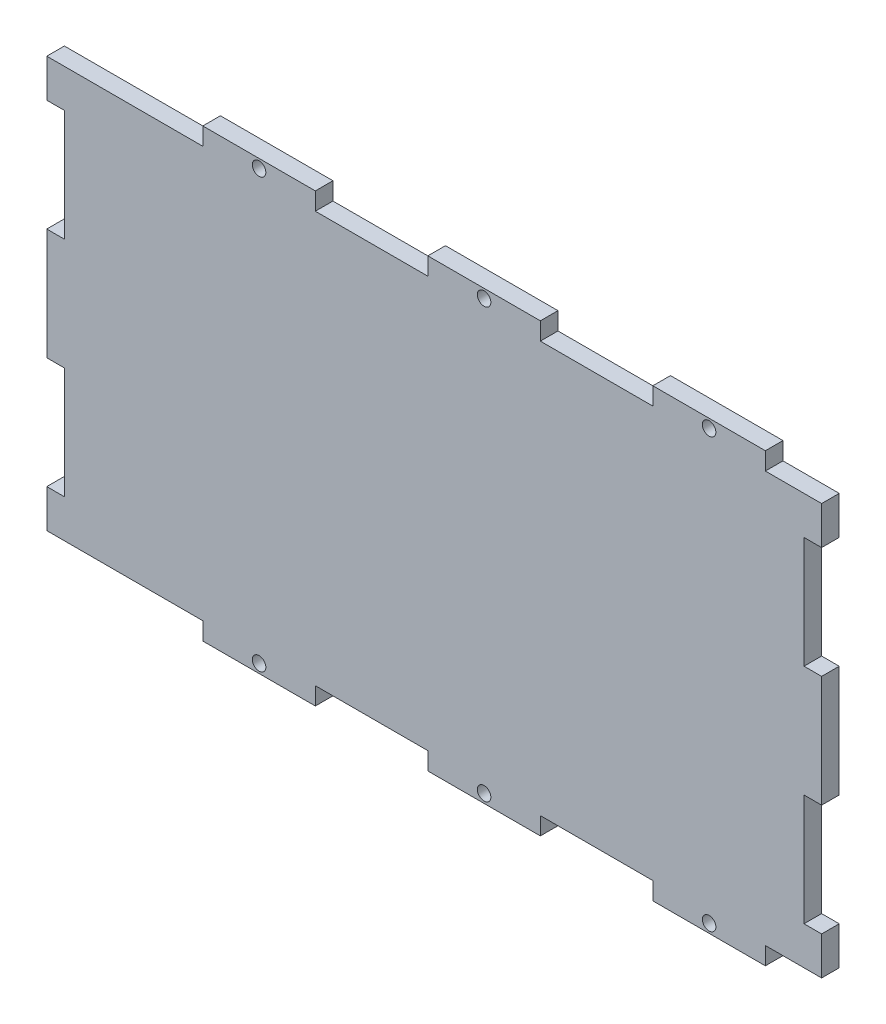
SolidWorks part; units mm, degrees
material "Acrílico (Impacto medio-alto)"
ref_plane "Alzado" through (0, 0, 0) normal (0, 0, 1) x (1, 0, 0)
ref_plane "Planta" through (0, 0, 0) normal (0, 1, 0) x (1, 0, 0)
ref_plane "Vista lateral" through (0, 0, 0) normal (1, 0, 0) x (0, 0, -1)
sketch "Croquis1" plane through (0, 0, 0) normal (0, 0, 1) x (1, 0, 0)
  line L1 (-57.5, -35) -> (57.5, -35)
  line L2 (-57.5, -35) -> (-57.5, 35)
  line L3 (-57.5, 35) -> (57.5, 35)
  line L4 (57.5, -35) -> (57.5, 35)
  line L5 (-57.5, -35) -> (57.5, 35) construction
  line L6 (-57.5, 35) -> (57.5, -35) construction
  point P0 (0, 0)
  dimension "D1" = 70
  dimension "D2" = 115
extrude "Saliente-Extruir1" add sketch "Croquis1" along normal mid plane 3
sketch "Croquis2" plane through (0, 0, 0) normal (0, 0, 1) x (1, 0, 0)
  line L0 (57.5, 35) -> (-57.5, 35) construction
  line L1 (-47.9167, 35) -> (-28.75, 35)
  line L2 (-47.9167, 35) -> (-47.9167, 38)
  line L3 (-47.9167, 38) -> (-28.75, 38)
  line L4 (-28.75, 35) -> (-28.75, 38)
  line L5 (-57.5, 35) -> (-57.5, -35) construction
  circle A0 centre (-38.3333, 36.5) radius 1.15
  point P11 (-28.75, 36.5)
  point P13 (-38.3333, 38)
  dimension "D1" = 3
  dimension "D4" = 2.3
  dimension "D2" = 19.1667
  dimension "D3" = 9.5833
extrude "Saliente-Extruir2" add sketch "Croquis2" along normal mid plane 3
pattern_linear "MatrizL1" count 3 spacing 38.3333 along (1, 0, 0) of "Saliente-Extruir2"
mirror "Simetría1" about plane through (0, 0, 0) normal (0, 1, 0) of "MatrizL1", "Saliente-Extruir2"
sketch "Croquis3" plane through (0, 0, 0) normal (0, 0, 1) x (1, 0, 0)
  line L0 (57.5, -35) -> (57.5, 35) construction
  line L1 (57.5, 28.5) -> (54.5, 28.5)
  line L2 (57.5, 28.5) -> (57.5, 9.5)
  line L3 (57.5, 9.5) -> (54.5, 9.5)
  line L4 (54.5, 28.5) -> (54.5, 20.15)
  line L5 (54.5, 17.85) -> (51.5, 17.85) construction
  line L6 (51.5, 17.85) -> (51.5, 20.15) construction
  line L7 (51.5, 20.15) -> (54.5, 20.15) construction
  line L8 (54.5, 17.85) -> (54.5, 9.5)
  line L9 (54.5, 20.15) -> (54.5, 17.85)
  line L10 (9.5833, 38) -> (-9.5833, 38) construction
  point P8 (51.5, 19)
  point P11 (57.5, 19)
  dimension "D1" = 2.3
  dimension "D2" = 3
  dimension "D3" = 3
  dimension "D5" = 19
  dimension "D4" = 9.5
extrude "Cortar-Extruir1" cut sketch "Croquis3" against normal through all both and the other way through all
pattern_linear "MatrizL2" count 2 spacing 38 along (0, -1, 0) of "Cortar-Extruir1"
mirror "Simetría2" about plane through (0, 0, 0) normal (1, 0, 0) of "MatrizL2", "Cortar-Extruir1"
sketch "Croquis4" plane through (-57.5, 0, 0) normal (-1, 0, 0) x (0, 0, 1)
  line L0 (1.5, -28.5) -> (-1.5, -28.5) construction
  line L1 (-1.5, -28.5) -> (-1.5, -35) construction
  line L2 (-1.5, -35) -> (1.5, -35) construction
  line L3 (1.5, -35) -> (1.5, -28.5) construction
  line L4 (-1.5, 28.5) -> (1.5, 28.5) construction
  line L5 (1.5, 28.5) -> (1.5, 35) construction
  line L6 (1.5, 35) -> (-1.5, 35) construction
  line L7 (-1.5, 35) -> (-1.5, 28.5) construction
  line L8 (1.5, 9.5) -> (-1.5, 9.5) construction
  line L9 (-1.5, 9.5) -> (-1.5, -9.5) construction
  line L10 (-1.5, -9.5) -> (1.5, -9.5) construction
  line L11 (1.5, -9.5) -> (1.5, 9.5) construction
  line L12 (1.5, -28.5) -> (-1.5, -28.5)
  line L13 (-1.5, -28.5) -> (-1.5, -35)
  line L14 (-1.5, -35) -> (1.5, -35)
  line L15 (1.5, -35) -> (1.5, -28.5)
  line L16 (-1.5, 28.5) -> (1.5, 28.5)
  line L17 (1.5, 28.5) -> (1.5, 35)
  line L18 (1.5, 35) -> (-1.5, 35)
  line L19 (-1.5, 35) -> (-1.5, 28.5)
  line L20 (1.5, 9.5) -> (-1.5, 9.5)
  line L21 (-1.5, 9.5) -> (-1.5, -9.5)
  line L22 (-1.5, -9.5) -> (1.5, -9.5)
  line L23 (1.5, -9.5) -> (1.5, 9.5)
extrude "Saliente-Extruir3" add sketch "Croquis4" along normal blind 17
sketch "Croquis5" plane through (-54.5, 0, 0) normal (-1, 0, 0) x (0, 0, 1)
  line L32 (1.5, -9.5) -> (-1.5, -9.5) construction
  line L33 (-1.5, -9.5) -> (-1.5, -28.5) construction
  line L34 (-1.5, -28.5) -> (1.5, -28.5) construction
  line L35 (1.5, -28.5) -> (1.5, -9.5) construction
  line L36 (1.5, 28.5) -> (-1.5, 28.5) construction
  line L37 (-1.5, 28.5) -> (-1.5, 9.5) construction
  line L38 (-1.5, 9.5) -> (1.5, 9.5) construction
  line L39 (1.5, 9.5) -> (1.5, 28.5) construction
  line L40 (1.5, -9.5) -> (-1.5, -9.5)
  line L41 (-1.5, -9.5) -> (-1.5, -28.5)
  line L42 (-1.5, -28.5) -> (1.5, -28.5)
  line L43 (1.5, -28.5) -> (1.5, -9.5)
  line L44 (1.5, 28.5) -> (-1.5, 28.5)
  line L45 (-1.5, 28.5) -> (-1.5, 9.5)
  line L46 (-1.5, 9.5) -> (1.5, 9.5)
  line L47 (1.5, 9.5) -> (1.5, 28.5)
extrude "Saliente-Extruir4" add sketch "Croquis5" along normal offset from surface (17 mm away) 3 up to face at (-74.5, 0, 0)
equation "\"grosor\"= 3mm'Acrilico"
equation "\"W\"= 109mm"
equation "\"H\"= 70mm"
equation "\"L\"= 70mm"
equation "\"D1@Croquis1\"=\"L\""
equation "\"cW\"= \"W\" + 2 * \"grosor\""
equation "\"D2@Croquis1\"=\"cW\""
equation "\"D1@Saliente-Extruir1\"=\"grosor\""
equation "\"D1@Croquis2\"=\"grosor\""
equation "\"longInstance\"= 3"
equation "\"D2@Croquis2\"=\"cW\"/(2*\"longInstance\")"
equation "\"D3@Croquis2\"=\"cW\"/(4*\"longInstance\")"
equation "\"D1@Saliente-Extruir2\"=\"grosor\""
equation "\"D1@MatrizL1\"=\"longInstance\""
equation "\"D3@MatrizL1\"=\"cW\"/(\"longInstance\")"
equation "\"wallInstance\"= 2"
equation "\"shortInstance\"= 2"
equation "\"D2@Croquis3\"=\"grosor\""
equation "\"D3@Croquis3\"=\"grosor\""
equation "\"D5@Croquis3\"=\"cL\"/(2*\"wallInstance\")"
equation "\"D1@MatrizL2\"=\"wallInstance\""
equation "\"D3@MatrizL2\"=\"cL\"/\"wallInstance\""
equation "\"cL\"= \"L\" + 2 * \"grosor\""
equation "\"D4@Croquis3\"=\"cL\"/(4*\"wallInstance\")"
equation "\"shortInsert\"= 62.23mm"
equation "\"MACHUELO\"=2.3"
equation "\"D4@Croquis2\"=\"MACHUELO\""
equation "\"D1@Croquis3\"=\"MACHUELO\""
equation "\"D1@Saliente-Extruir4\"=\"grosor\""
equation "\"D1@Saliente-Extruir5\"=\"grosor\""
